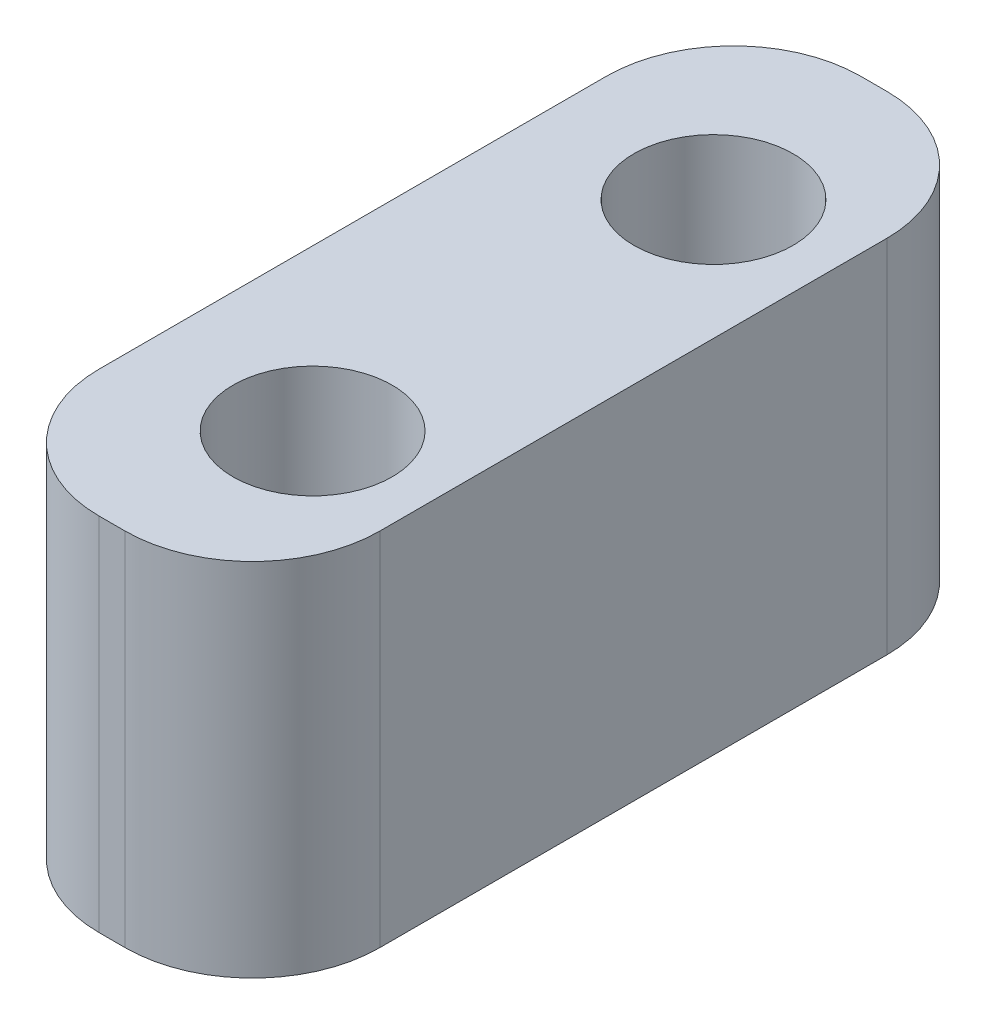
SolidWorks part; units mm, degrees
ref_plane "Front Plane" through (0, 0, 0) normal (0, 0, 1) x (1, 0, 0)
ref_plane "Top Plane" through (0, 0, 0) normal (0, 1, 0) x (1, 0, 0)
ref_plane "Right Plane" through (0, 0, 0) normal (1, 0, 0) x (0, 0, -1)
sketch "Sketch1" plane through (0, 0, 0) normal (0, 0, 1) x (1, 0, 0)
  line L1 (0, 0) -> (7, 0)
  line L2 (0, 0) -> (0, 9)
  line L3 (0, 9) -> (7, 9)
  line L4 (7, 0) -> (7, 9)
  dimension "D1" = 9
  dimension "D2" = 7
extrude "Boss-Extrude1" add sketch "Sketch1" along normal blind 19
sketch "Sketch2" plane through (0, 9, 0) normal (0, 1, 0) x (1, 0, 0)
  line L0 (7, -19) -> (7, 0) construction
  line L1 (7, -19) -> (7, 0) construction
  line L2 (4, -4.5) -> (4, -14.5) construction
  circle A0 centre (4, -4.5) radius 1.9844
  circle A1 centre (4, -14.5) radius 1.9844
  point P4 (4, -9.5)
  point P5 (7, -9.5)
  dimension "D3" = 3.9688
  dimension "D4" = 3.9688
  dimension "D1" = 3
  dimension "D2" = 10
extrude "Cut-Extrude1" cut sketch "Sketch2" against normal up to surface (9 mm away) up to face at (3.5, 0, 9.5)
fillet "Fillet1" radius 3.175 4 edges at (0, 4.5, 0) (7, 4.5, 0) (7, 4.5, 19) (0, 4.5, 19)
